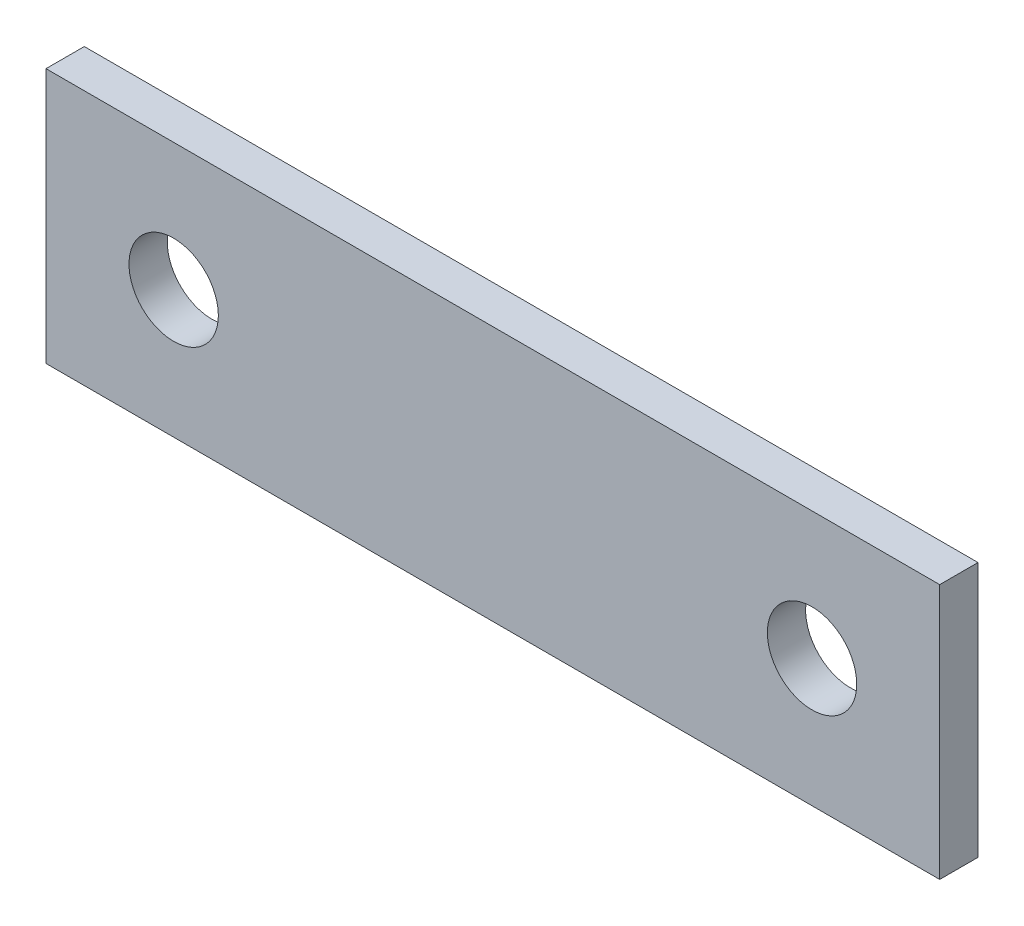
SolidWorks part; units mm, degrees
material "Acrílico (Impacto medio-alto)"
ref_plane "Alzado" through (0, 0, 0) normal (0, 0, 1) x (1, 0, 0)
ref_plane "Planta" through (0, 0, 0) normal (0, 1, 0) x (1, 0, 0)
ref_plane "Vista lateral" through (0, 0, 0) normal (1, 0, 0) x (0, 0, -1)
sketch "Croquis1" plane through (0, 0, 0) normal (0, 0, 1) x (1, 0, 0)
  line L1 (-81.8885, 26.0053) -> (-11.8885, 26.0053)
  line L2 (-81.8885, 26.0053) -> (-81.8885, 6.0053)
  line L3 (-81.8885, 6.0053) -> (-11.8885, 6.0053)
  line L4 (-11.8885, 26.0053) -> (-11.8885, 6.0053)
  circle A0 centre (-71.8885, 16.0053) radius 3.5
  circle A1 centre (-21.8885, 16.0053) radius 3.5
  dimension "D3" = 10
  dimension "D1" = 70
  dimension "D2" = 20
  dimension "D4" = 10
  dimension "D5" = 10
  dimension "D6" = 10
extrude "Saliente-Extruir1" add sketch "Croquis1" along normal blind 3
